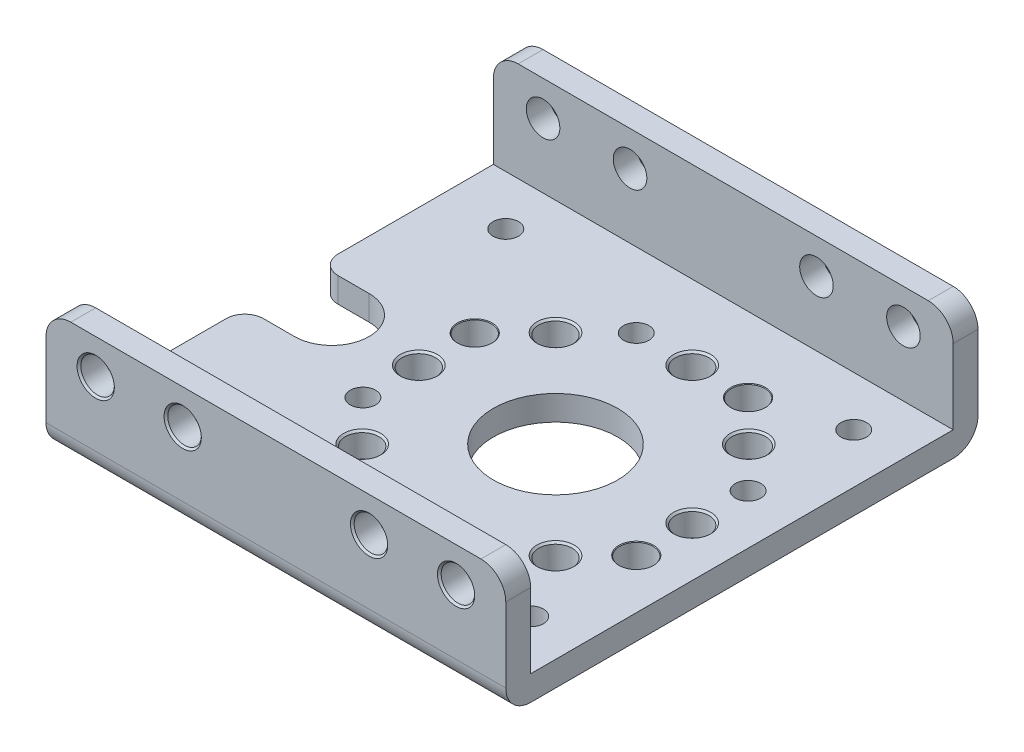
SolidWorks part; units mm, degrees
ref_plane "Front Plane" through (0, 0, 0) normal (0, 0, 1) x (1, 0, 0)
ref_plane "Top Plane" through (0, 0, 0) normal (0, 1, 0) x (1, 0, 0)
ref_plane "Right Plane" through (0, 0, 0) normal (1, 0, 0) x (0, 0, -1)
ref_plane "Plane1" through (0, 10, 0) normal (0, 1, 0) x (1, 0, 0)
sketch "Sketch1" plane through (0, 10, 0) normal (0, 1, 0) x (1, 0, 0)
  line L0 (-22, -19) -> (15, -19)
  line L1 (15, -19) -> (15, 19)
  line L2 (15, 19) -> (-22, 19)
  line L3 (-22, 19) -> (-22, -19)
extrude "Boss-Extrude1" add sketch "Sketch1" against normal blind 10
sketch "Sketch2" plane through (15, 0, 0) normal (1, 0, 0) x (0, 0, -1)
  line L0 (17, 10) -> (-17, 10)
  line L1 (-17, 10) -> (-17, 2)
  line L2 (-17, 2) -> (17, 2)
  line L3 (17, 2) -> (17, 10)
extrude "Cut-Extrude1" cut sketch "Sketch2" against normal through all
sketch "Sketch3" plane through (0, 2, 0) normal (0, 1, 0) x (-1, 0, 0)
  line L0 (22, -3) -> (22, 3)
  line L1 (22, 3) -> (18, 3)
  line L2 (18, -3) -> (22, -3)
  arc A0 (18, 3) -> (18, -3) centre (18, 0) ccw
extrude "Cut-Extrude2" cut sketch "Sketch3" against normal through all
hole_wizard "Ø2.05 (2.05) Diameter Hole1" positions "Sketch5" profile "Sketch4" hole size "Ø2.05" standard "ANSI Metric"
sketch "Sketch5" plane through (0, 0, 0) normal (0, -1, 0) x (-1, 0, 0)
  point P0 (-11, 13)
  point P1 (-11, -13)
  point P2 (17, 13)
  point P3 (17, -13)
  point P4 (-11, 4.5)
  point P5 (-4.5, -11)
  point P6 (11, -4.5)
  point P7 (4.5, 11)
sketch "Sketch4" plane through (11, 0, -13) normal (1, 0, 0) x (0, 0, -1)
  line L0 (0, 0) -> (0, 10)
  line L1 (0, 10) -> (1.025, 10)
  line L2 (1.025, 10) -> (1.025, 0)
  line L5 (1.025, 0) -> (0, 0)
  line L11 (0, -6.35) -> (0, 107.95) construction
  dimension "Thru Hole Dia." = 2.05
  dimension "Thru Hole Depth" = 10
hole_wizard "Ø10.0 (10) Diameter Hole1" positions "Sketch7" profile "Sketch6" hole size "Ø10.0" standard "ANSI Metric"
sketch "Sketch7" plane through (0, 0, 0) normal (0, -1, 0) x (-1, 0, 0)
  point P0 (0, 0)
sketch "Sketch6" plane through (0, 0, 0) normal (1, 0, 0) x (0, 0, -1)
  line L0 (0, 0) -> (0, 10)
  line L1 (0, 10) -> (5, 10)
  line L2 (5, 10) -> (5, 0)
  line L5 (5, 0) -> (0, 0)
  line L11 (0, -6.35) -> (0, 107.95) construction
  dimension "Thru Hole Dia." = 10
  dimension "Thru Hole Depth" = 10
hole_wizard "Ø2.7 (2.7) Diameter Hole1" positions "Sketch9" profile "Sketch8" hole size "Ø2.7" standard "ANSI Metric"
sketch "Sketch9" plane through (0, 2, 0) normal (0, 1, 0) x (1, 0, 0)
  point P0 (11, 0)
  point P1 (7.7782, 7.7782)
  point P2 (0, 11)
  point P3 (-7.7782, 7.7782)
  point P4 (-11, 0)
  point P5 (-7.7782, -7.7782)
  point P6 (0, -11)
  point P7 (7.7782, -7.7782)
  point P8 (4.5, 11)
  point P9 (11, -4.5)
  point P10 (-4.5, -11)
  point P11 (-11, 4.5)
sketch "Sketch8" plane through (11, 2, 0) normal (1, 0, 0) x (0, 0, 1)
  line L0 (0, 0) -> (0, 2)
  line L1 (0, 2) -> (1.35, 2)
  line L2 (1.35, 2) -> (1.35, 0)
  line L5 (1.35, 0) -> (0, 0)
  line L11 (0, -6.35) -> (0, 107.95) construction
  dimension "Thru Hole Dia." = 2.7
  dimension "Thru Hole Depth" = 2
hole_wizard "Ø2.7 (2.7) Diameter Hole2" positions "Sketch11" profile "Sketch10" hole size "Ø2.7" standard "ANSI Metric"
sketch "Sketch11" plane through (0, 0, 19) normal (0, 0, 1) x (1, 0, 0)
  point P0 (4, 7.2)
  point P1 (-18, 7.2)
  point P2 (11, 7.2)
  point P3 (-11, 7.2)
sketch "Sketch10" plane through (4, 7.2, 19) normal (1, 0, 0) x (0, -1, 0)
  line L0 (0, 0) -> (0, 2)
  line L1 (0, 2) -> (1.35, 2)
  line L2 (1.35, 2) -> (1.35, 0)
  line L5 (1.35, 0) -> (0, 0)
  line L11 (0, -6.35) -> (0, 107.95) construction
  dimension "Thru Hole Dia." = 2.7
  dimension "Thru Hole Depth" = 2
hole_wizard "Ø2.7 (2.7) Diameter Hole3" positions "Sketch13" profile "Sketch12" hole size "Ø2.7" standard "ANSI Metric"
sketch "Sketch13" plane through (0, 0, -19) normal (0, 0, -1) x (-1, 0, 0)
  point P0 (-4, 7.2)
  point P1 (18, 7.2)
  point P2 (-11, 7.2)
  point P3 (11, 7.2)
sketch "Sketch12" plane through (4, 7.2, -19) normal (1, 0, 0) x (0, 1, 0)
  line L0 (0, 0) -> (0, 38)
  line L1 (0, 38) -> (1.35, 38)
  line L2 (1.35, 38) -> (1.35, 0)
  line L5 (1.35, 0) -> (0, 0)
  line L11 (0, -6.35) -> (0, 107.95) construction
  dimension "Thru Hole Dia." = 2.7
  dimension "Thru Hole Depth" = 38
chamfer "Chamfer1" distance 0.15 angle 45 16 edges at (7.7782, 2, 9.1282) (12.35, 7.2, 19) (-7.7782, 2, 9.1282) (5.35, 7.2, 19) (0, 2, 12.35) (-19.35, 7.2, -19) (-12.35, 7.2, -19) (9.65, 7.2, -19) (-16.65, 7.2, 19) (0, 2, -9.65) (-9.65, 7.2, 19) (-7.7782, 2, -6.4282) (-11, 2, 1.35) (11, 2, 1.35) (2.65, 7.2, -19) (7.7782, 2, -6.4282)
chamfer "Chamfer2" distance 0.05 angle 45 4 edges at (-11, 2, -3.15) (11, 2, 5.85) (4.5, 2, -9.65) (-4.5, 2, 12.35)
chamfer "Chamfer3" distance 0.375 angle 45 8 edges at (11, 0, 11.975) (-17, 0, -14.025) (-17, 0, 11.975) (11, 0, -5.525) (11, 0, -14.025) (4.5, 0, 9.975) (-11, 0, 3.475) (-4.5, 0, -12.025)
fillet "Fillet1" radius 1.5 2 edges at (-22, 1, 3) (-22, 1, -3)
fillet "Fillet2" radius 2 6 edges at (-3.5, 0, 19) (15, 10, -18) (-22, 10, -18) (-22, 10, 18) (15, 10, 18) (-3.5, 0, -19)
